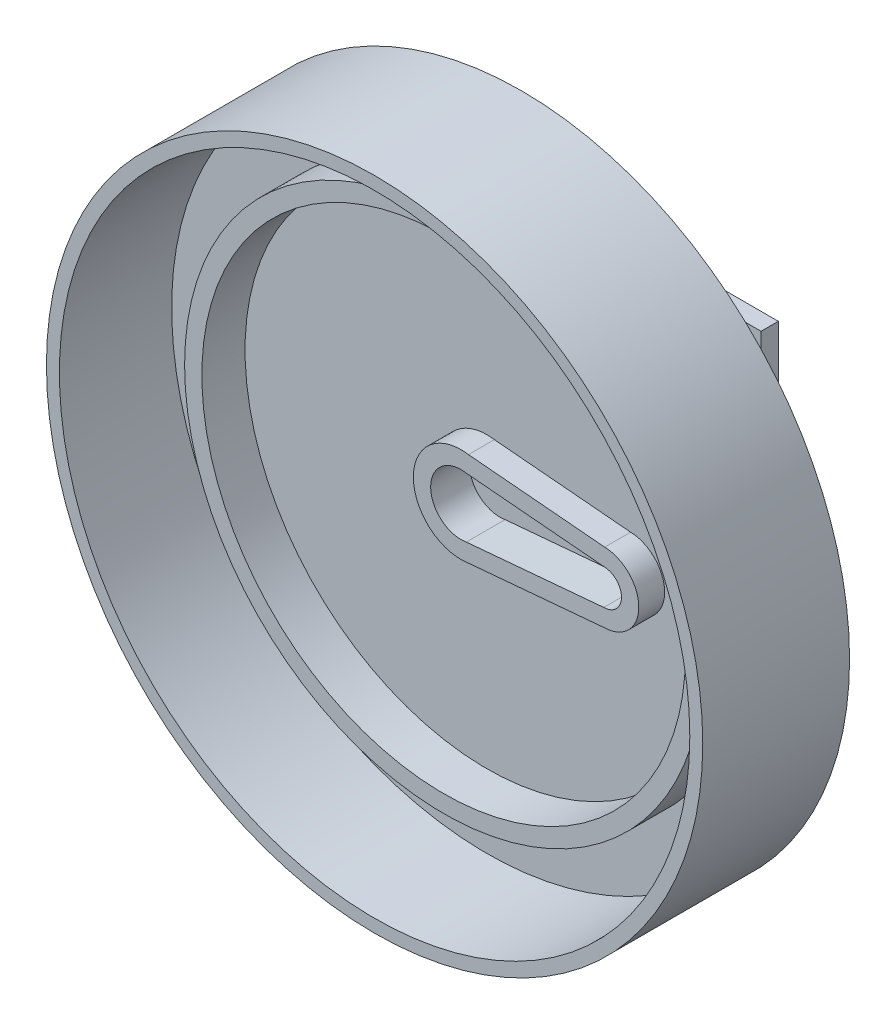
SolidWorks part; units mm, degrees
ref_plane "Front Plane" through (0, 0, 0) normal (0, 0, 1) x (1, 0, 0)
ref_plane "Top Plane" through (0, 0, 0) normal (0, 1, 0) x (1, 0, 0)
ref_plane "Right Plane" through (0, 0, 0) normal (1, 0, 0) x (0, 0, -1)
sketch "Sketch2" plane through (0, 0, 0) normal (0, 0, 1) x (1, 0, 0)
  circle A0 centre (0, 0) radius 38
  circle A1 centre (0, 0) radius 28
  circle A2 centre (0, 0) radius 30
  circle A3 centre (0, 0) radius 36.5
extrude "Boss-Extrude1" add sketch "Sketch2" along normal blind 5 contours A2 A1 | A0 A3
sketch "Sketch3" plane through (0, 0, 0) normal (0, 0, -1) x (-1, 0, 0)
  circle A0 centre (0, 0) radius 38
sketch "Sketch5" plane through (0, 0, 0) normal (0, 0, -1) x (-1, 0, 0)
  circle A0 centre (0, 0) radius 38
extrude "Boss-Extrude2" add sketch "Sketch5" along normal blind 4
sketch "Sketch6" plane through (0, 0, 0) normal (0, 0, 1) x (1, 0, 0)
  line L0 (0.8686, 5.4411) -> (16.6429, 4.0487)
  line L1 (0.6149, 3.4557) -> (16.54, 2.05)
  line L2 (16.6429, -4.0487) -> (0.8686, -5.4411)
  line L3 (16.54, -2.05) -> (0.6149, -3.4557)
  arc A0 (0.6149, 3.4557) -> (0.6149, -3.4557) centre (0, 0) ccw
  arc A1 (16.54, -2.05) -> (16.54, 2.05) centre (16.54, 0) ccw
  arc A2 (16.6429, -4.0487) -> (16.6429, 4.0487) centre (16.54, 0) ccw
  arc A3 (0.8686, 5.4411) -> (0.8686, -5.4411) centre (0, 0) ccw
  dimension "D1" = 2
extrude "Boss-Extrude3" add sketch "Sketch6" along normal blind 3 contours L0 A2 L2 A3 | L3 A0 L1 A1
sketch "Sketch9" plane through (0, 0, 0) normal (0, 0, 1) x (1, 0, 0)
  line L1 (0.6149, 3.4557) -> (16.54, 2.05)
  line L3 (16.54, -2.05) -> (0.6149, -3.4557)
  arc A0 (0.6149, 3.4557) -> (0.6149, -3.4557) centre (0, 0) ccw
  arc A1 (16.54, -2.05) -> (16.54, 2.05) centre (16.54, 0) ccw
extrude "Cut-Extrude1" cut sketch "Sketch9" against normal blind 1.5
sketch "Sketch10" plane through (0, 0, 5) normal (0, 0, 1) x (1, 0, 0)
  circle A0 centre (0, 0) radius 36.5
  circle A1 centre (0, 0) radius 38
extrude "Boss-Extrude4" add sketch "Sketch10" along normal blind 8
sketch "Sketch11" plane through (0, 0, -4) normal (0, 0, -1) x (-1, 0, 0)
  line L1 (-10, 10) -> (10, 10)
  line L2 (-10, 10) -> (-10, -10)
  line L3 (-10, -10) -> (10, -10)
  line L4 (10, 10) -> (10, -10)
  line L5 (-10, 10) -> (10, -10) construction
  line L6 (-10, -10) -> (10, 10) construction
  point P0 (0, 0)
extrude "Boss-Extrude5" add sketch "Sketch11" along normal blind 8
sketch "Sketch12" plane through (0, 0, -12) normal (0, 0, -1) x (-1, 0, 0)
  line L1 (-19.75, 19.75) -> (19.75, 19.75)
  line L2 (-19.75, 19.75) -> (-19.75, -19.75)
  line L3 (-19.75, -19.75) -> (19.75, -19.75)
  line L4 (19.75, 19.75) -> (19.75, -19.75)
  line L5 (-19.75, 19.75) -> (19.75, -19.75) construction
  line L6 (-19.75, -19.75) -> (19.75, 19.75) construction
  point P0 (0, 0)
extrude "Boss-Extrude6" add sketch "Sketch12" along normal blind 2
